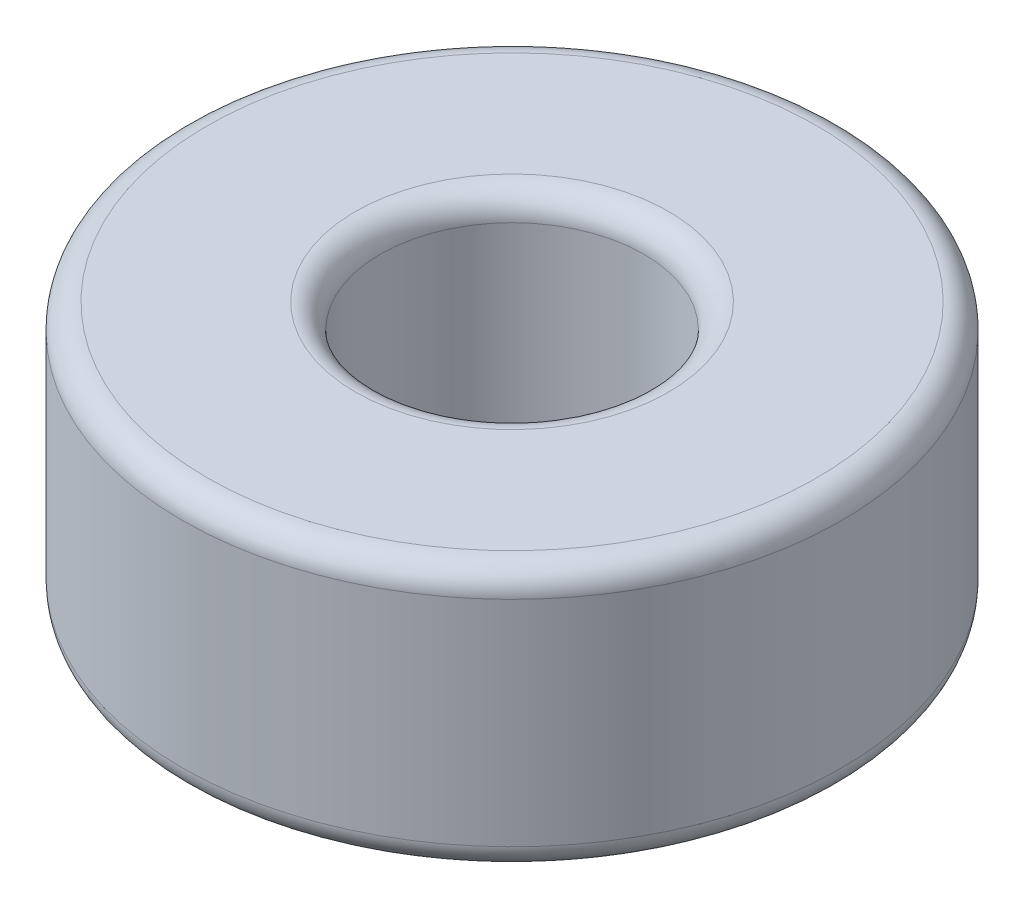
SolidWorks part; units mm, degrees
ref_plane "Front Plane" through (0, 0, 0) normal (0, 0, 1) x (1, 0, 0)
ref_plane "Top Plane" through (0, 0, 0) normal (0, 1, 0) x (1, 0, 0)
ref_plane "Right Plane" through (0, 0, 0) normal (1, 0, 0) x (0, 0, -1)
sketch "Sketch1" plane through (0, 0, 0) normal (0, 1, 0) x (1, 0, 0)
  circle A0 centre (0, 0) radius 5
  dimension "D1" = 10
extrude "Boss-Extrude1" add sketch "Sketch1" along normal mid plane 4
sketch "Sketch2" plane through (0, 0, 0) normal (0, 1, 0) x (1, 0, 0)
  circle A0 centre (0, 0) radius 2
  dimension "D1" = 4
extrude "Cut-Extrude1" cut sketch "Sketch2" against normal through all both and the other way through all
fillet "Fillet1" radius 0.375 4 edges at (0, -2, 5) (0, -2, 2) (0, 2, 5) (0, 2, 2)
equation "\"D1@Boss-Extrude1\" = \"ARM Both Nema Bearing Thickness\""
equation "\"D1@Sketch2\" = \"ARM Both Nema Shaft Dia\""
equation "\"D1@Sketch1\" = \"ARM Both Nema Bearing ID\""
equation "\"D1@Fillet1\"= \"ALL Small Fillet\" * ( 3 / 4 )"
equation "\"ALL Big Fillet\"= 10.0mm"
equation "\"ALL Medium Fillet\"= 1.0mm"
equation "\"ALL Small Fillet\"= 0.5mm"
equation "\"BODY Rad\"= 82.5mm"
equation "\"BODY End Cut Rad\"= 72.5mm"
equation "\"BODY Height Ext\"= 27.5mm"
equation "\"BODY Bottom Cut Dist\"= 50.0mm"
equation "\"BODY Seal Thickness\"= 3.75mm"
equation "\"BODY Wall Extra Thickness\"= 2.5mm"
equation "\"BODY Bottom Extra Nut Wall\"= 7.5mm"
equation "\"ARM Both Dia\"= 39.75mm"
equation "\"ARM Both Length\"= 67.5mm"
equation "\"ARM Both Wire Hole Dia\"= 15.0mm"
equation "\"ARM Both Prop Seal Thickness\"= 2.5mm"
equation "\"ARM Both Brass Insert Dia\"= 4.875mm"
equation "\"ARM Both Bolt Cut Depth\"= 12.5mm"
equation "\"ARM Both Nema Bolt Off\"= 15.4mm"
equation "\"ARM Both Nema Bolt Depth\"= 2.5mm"
equation "\"ARM Both Nema Width\"= 20.0mm"
equation "\"ARM Both Nema Wall Off\"= 2.5mm"
equation "\"ARM Both Nema Center Dia 1\"= 17.0mm"
equation "\"ARM Both Nema Center Dia 2\"= 10.0mm"
equation "\"ARM Both Nema Bearing OD\"= 16.0mm"
equation "\"ARM Both Nema Bearing ID\"= 10.0mm"
equation "\"ARM Both Nema Bearing Thickness\"= 4.0mm"
equation "\"ARM Both Nema Height\"= 38.0mm"
equation "\"ARM Both Nema Shaft Dia\"= 4.0mm"
equation "\"ARM Both Nema Shaft Length\"= 10.0mm"
equation "\"ARM Both Nema Center Height\"= 1.5mm"
equation "\"ARM Rotating Bearing OD\"= 68.0mm"
equation "\"ARM Rotating Bearing ID\"= 40.0mm"
equation "\"ARM Rotating Bearing Thickness\"= 15.0mm"
equation "\"ARM Static Mount Dia\"= 65.0mm"
equation "\"ARM Static Bolt Off\"= 1.125mm"
equation "\"ALL Bolt Hole Off\"= 0.25mm"
equation "\"ALL Vert Bolt Hole Off Scalar\"= 0.5mm"
equation "\"ALL Horz Bolt Hole Off Scalar\"= 1.25mm"
equation "\"ALL Nut Size Off\"= 0.25mm"
equation "\"ALL Vert Nut Off Scalar\"= 0.5mm"
equation "\"ALL Horz Nut Off Scalar\"= 1.25mm"
equation "\"BODY Bolt Count\"= 12"
equation "\"BODY Bolt Size\"= 6"
equation "\"BODY Bolt Length\"= 22.0mm"
equation "\"BODY Bolt Head Dia\"= IIF ( \"BODY Bolt Size\" = 3 , 5.75mm , IIF ( \"BODY Bolt Size\" = 4 , 7.25mm , IIF ( \"BODY Bolt Size\" = 5 , 8.75mm , IIF ( \"BODY Bolt Size\" = 6 , 10.25mm , 5.75mm ) ) ) )"
equation "\"BODY Bolt Head Height\"= IIF ( \"BODY Bolt Size\" = 3 , 3.0mm , IIF ( \"BODY Bolt Size\" = 4 , 4.0mm , IIF ( \"BODY Bolt Size\" = 5 , 5.0mm , IIF ( \"BODY Bolt Size\" = 6 , 6.0mm , 3.0mm ) ) ) )"
equation "\"BODY Nut Width\"= IIF ( \"BODY Bolt Size\" = 3 , 5.5mm , IIF ( \"BODY Bolt Size\" = 4 , 7.0mm , IIF ( \"BODY Bolt Size\" = 5 , 8.0mm , IIF ( \"BODY Bolt Size\" = 6 , 10.0mm , 5.5mm ) ) ) )"
equation "\"BODY Nut Height\"= IIF ( \"BODY Bolt Size\" = 3 , 4.0mm , IIF ( \"BODY Bolt Size\" = 4 , 5.0mm , IIF ( \"BODY Bolt Size\" = 5 , 5.0mm , IIF ( \"BODY Bolt Size\" = 6 , 6.0mm , 4.0mm ) ) ) )"
equation "\"ARM Static Bolt Count\"= 8"
equation "\"ARM Static Bolt Size\"= 5"
equation "\"ARM Static Bolt Length\"= 20.0mm"
equation "\"ARM Static Bolt Head Dia\"= IIF ( \"ARM Static Bolt Size\" = 3 , 5.75mm , IIF ( \"ARM Static Bolt Size\" = 4 , 7.25mm , IIF ( \"ARM Static Bolt Size\" = 5 , 8.75mm , IIF ( \"ARM Static Bolt Size\" = 6 , 10.25mm , 5.75mm ) ) ) )"
equation "\"ARM Static Bolt Head Height\"= IIF ( \"ARM Static Bolt Size\" = 3 , 3.0mm , IIF ( \"ARM Static Bolt Size\" = 4 , 4.0mm , IIF ( \"ARM Static Bolt Size\" = 5 , 5.0mm , IIF ( \"ARM Static Bolt Size\" = 6 , 6.0mm , 3.0mm ) ) ) )"
equation "\"ARM Static Nut Width\"= IIF ( \"ARM Static Bolt Size\" = 3 , 5.5mm , IIF ( \"ARM Static Bolt Size\" = 4 , 7.0mm , IIF ( \"ARM Static Bolt Size\" = 5 , 8.0mm , IIF ( \"ARM Static Bolt Size\" = 6 , 10.0mm , 5.5mm ) ) ) )"
equation "\"ARM Static Nut Height\"= IIF ( \"ARM Static Bolt Size\" = 3 , 4.0mm , IIF ( \"ARM Static Bolt Size\" = 4 , 5.0mm , IIF ( \"ARM Static Bolt Size\" = 5 , 5.0mm , IIF ( \"ARM Static Bolt Size\" = 6 , 6.0mm , 4.0mm ) ) ) )"
equation "\"ARM Gear Width\"= 10.0mm"
equation "\"ARM Gear Width Off\"= 2.5mm"
equation "\"ARM Gear Bolt Count\"= 4"
equation "\"ARM Gear Rotation\"= 360.0deg"
equation "\"ARM Gear Bolt Size\"= 3"
equation "\"ARM Gear Bolt Length\"= 20.0mm"
equation "\"ARM Gear Bolt Head Dia\"= IIF ( \"ARM Static Bolt Size\" = 3 , 5.75mm , IIF ( \"ARM Static Bolt Size\" = 4 , 7.25mm , IIF ( \"ARM Static Bolt Size\" = 5 , 8.75mm , IIF ( \"ARM Static Bolt Size\" = 6 , 10.25mm , 5.75mm ) ) ) )"
equation "\"ARM Gear Bolt Head Height\"= IIF ( \"ARM Static Bolt Size\" = 3 , 3.0mm , IIF ( \"ARM Static Bolt Size\" = 4 , 4.0mm , IIF ( \"ARM Static Bolt Size\" = 5 , 5.0mm , IIF ( \"ARM Static Bolt Size\" = 6 , 6.0mm , 3.0mm ) ) ) )"
equation "\"ARM Gear Nut Width\"= IIF ( \"ARM Static Bolt Size\" = 3 , 5.5mm , IIF ( \"ARM Static Bolt Size\" = 4 , 7.0mm , IIF ( \"ARM Static Bolt Size\" = 5 , 8.0mm , IIF ( \"ARM Static Bolt Size\" = 6 , 10.0mm , 5.5mm ) ) ) )"
equation "\"ARM Gear Nut Height\"= IIF ( \"ARM Static Bolt Size\" = 3 , 4.0mm , IIF ( \"ARM Static Bolt Size\" = 4 , 5.0mm , IIF ( \"ARM Static Bolt Size\" = 5 , 5.0mm , IIF ( \"ARM Static Bolt Size\" = 6 , 6.0mm , 4.0mm ) ) ) )"
equation "\"ARM Both Prop Plate Bolt Size\"= 3"
equation "\"ARM Both Prop Plate Bolt Length\"= 16.0mm"
equation "\"ARM Both Prop Plate Bolt Head Dia\"= IIF ( \"ARM Both Prop Plate Bolt Size\" = 3 , 5.75mm , IIF ( \"ARM Both Prop Plate Bolt Size\" = 4 , 7.25mm , IIF ( \"ARM Both Prop Plate Bolt Size\" = 5 , 8.75mm , IIF ( \"ARM Both Prop Plate Bolt Size\" = 6 , 10.25mm , 5.75mm ) ) ) )"
equation "\"ARM Both Prop Plate Bolt Head Height\"= IIF ( \"ARM Both Prop Plate Bolt Size\" = 3 , 3.0mm , IIF ( \"ARM Both Prop Plate Bolt Size\" = 4 , 4.0mm , IIF ( \"ARM Both Prop Plate Bolt Size\" = 5 , 5.0mm , IIF ( \"ARM Both Prop Plate Bolt Size\" = 6 , 6.0mm , 3.0mm ) ) ) )"
equation "\"ARM Both Nema Bolt Size\"= 2"
equation "\"ARM Both Nema Bolt Head Dia\"= IIF ( \"ARM Both Nema Bolt Size\" = 3 , 5.75mm , IIF ( \"ARM Both Nema Bolt Size\" = 4 , 7.25mm , IIF ( \"ARM Both Nema Bolt Size\" = 5 , 8.75mm , IIF ( \"ARM Both Nema Bolt Size\" = 6 , 10.25mm , 5.75mm ) ) ) )"
equation "\"ARM Both Nema Bolt Head Height\"= IIF ( \"ARM Both Nema Bolt Size\" = 3 , 3.0mm , IIF ( \"ARM Both Nema Bolt Size\" = 4 , 4.0mm , IIF ( \"ARM Both Nema Bolt Size\" = 5 , 5.0mm , IIF ( \"ARM Both Nema Bolt Size\" = 6 , 6.0mm , 3.0mm ) ) ) )"
